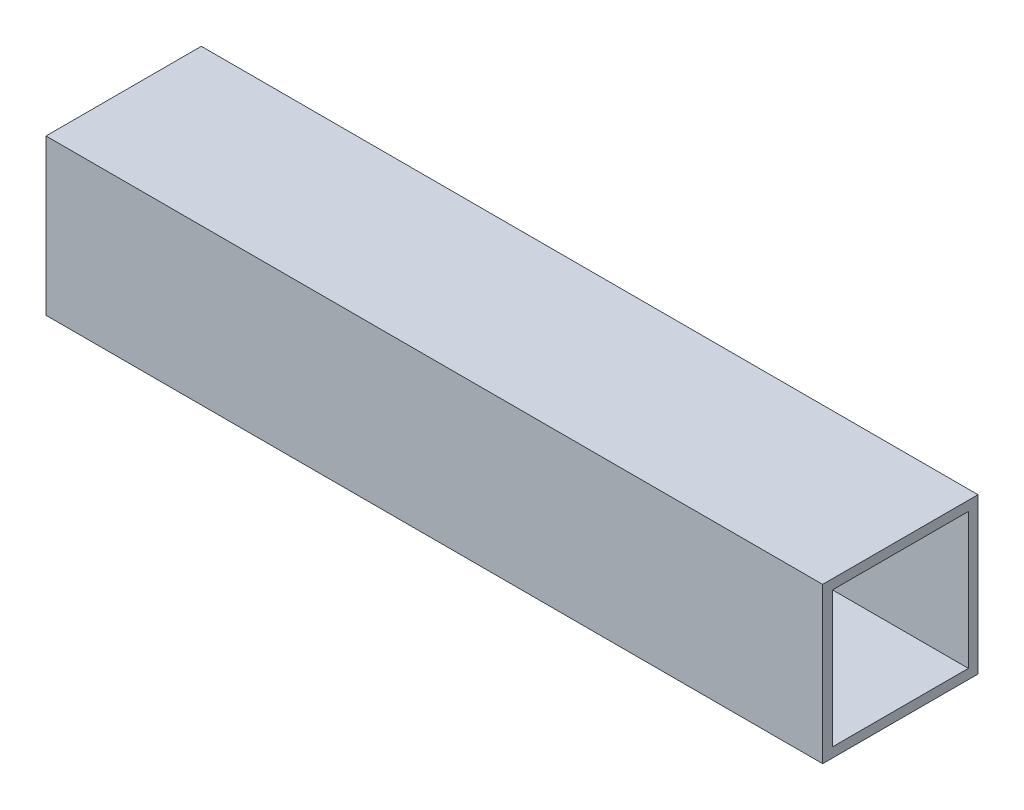
SolidWorks part; units mm, degrees
ref_plane "Front Plane" through (0, 0, 0) normal (0, 0, 1) x (1, 0, 0)
ref_plane "Top Plane" through (0, 0, 0) normal (0, 1, 0) x (1, 0, 0)
ref_plane "Right Plane" through (0, 0, 0) normal (1, 0, 0) x (0, 0, -1)
sketch "Sketch2" plane through (0, 0, 0) normal (1, 0, 0) x (0, 0, -1)
  line L1 (0, 0) -> (50.8, 0)
  line L2 (0, 0) -> (0, 50.8)
  line L3 (0, 50.8) -> (50.8, 50.8)
  line L4 (50.8, 0) -> (50.8, 50.8)
  line L5 (3.175, 47.625) -> (47.6631, 47.625)
  line L6 (3.175, 47.625) -> (3.175, 3.175)
  line L7 (3.175, 3.175) -> (47.6631, 3.175)
  line L8 (47.6631, 47.625) -> (47.6631, 3.175)
  dimension "D1" = 3.175
  dimension "D2" = 3.175
  dimension "D3" = 3.1369
  dimension "D4" = 3.175
  dimension "D5" = 50.8
  dimension "D6" = 50.8
extrude "Boss-Extrude1" add sketch "Sketch2" along normal blind 254
